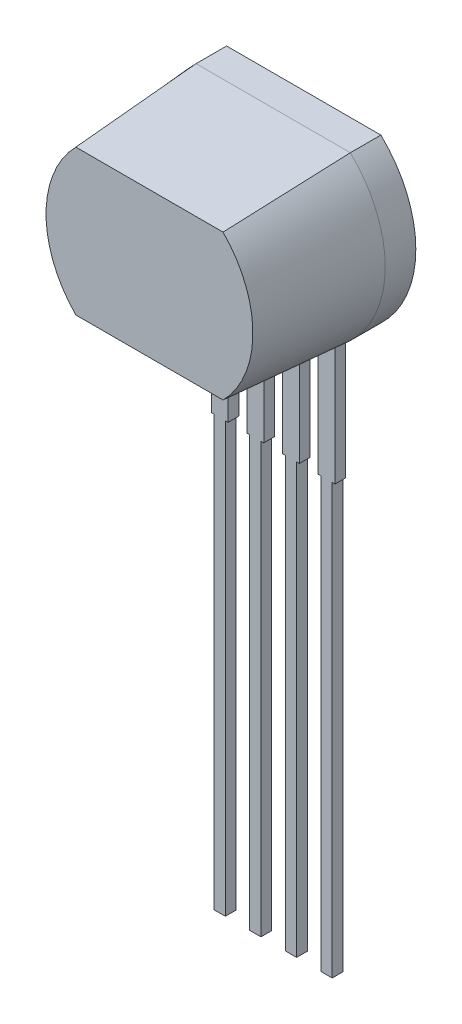
SolidWorks part; units mm, degrees
material "6061-T6 (SS)"
ref_plane "Front Plane" through (0, 0, 0) normal (0, 0, 1) x (1, 0, 0)
ref_plane "Top Plane" through (0, 0, 0) normal (0, 1, 0) x (1, 0, 0)
ref_plane "Right Plane" through (0, 0, 0) normal (1, 0, 0) x (0, 0, -1)
sketch "Sketch1" plane through (0, 0, 0) normal (0, 0, 1) x (1, 0, 0)
  line L0 (-2.75, 2.9) -> (2.75, 2.9)
  line L1 (0, 0) -> (6.1651, 0) construction
  line L2 (0, 0) -> (0, 2.9) construction
  line L3 (-2.75, -2.9) -> (2.75, -2.9)
  arc A0 (-2.75, 2.9) -> (-2.75, -2.9) centre (0.005, 0) ccw
  arc A1 (2.75, 2.9) -> (2.75, -2.9) centre (-0.005, 0) cw
  dimension "D1" = 4
  dimension "D2" = 5.5
  dimension "D3" = 5.8
extrude "Boss-Extrude1" add sketch "Sketch1" along normal blind 4.41 draft 4 and the other way blind 1.09
sketch "Sketch2" plane through (0, 0, 0) normal (0, 0, 1) x (1, 0, 0)
  line L0 (-2.75, -2.9) -> (2.75, -2.9) construction
  line L1 (2.205, -2.9) -> (1.605, -2.9)
  line L2 (2.205, -2.9) -> (2.205, -7.6)
  line L3 (2.205, -7.6) -> (1.605, -7.6) construction
  line L4 (1.605, -2.9) -> (1.605, -7.6)
  line L5 (0.935, -2.9) -> (0.335, -2.9)
  line L6 (0.935, -2.9) -> (0.935, -7.6)
  line L7 (0.335, -2.9) -> (0.335, -7.6)
  line L8 (0.835, -7.6) -> (0.835, -22.9)
  line L9 (0.835, -7.6) -> (0.435, -7.6) construction
  line L10 (0.835, -22.9) -> (0.435, -22.9)
  line L11 (0.435, -7.6) -> (0.435, -22.9)
  line L12 (0.835, -7.6) -> (0.935, -7.6)
  line L13 (0.435, -7.6) -> (0.335, -7.6)
  line L14 (0.935, -7.6) -> (0.335, -7.6) construction
  line L15 (-0.335, -2.9) -> (-0.935, -2.9)
  line L16 (-0.335, -2.9) -> (-0.335, -7.6)
  line L17 (-0.935, -2.9) -> (-0.935, -7.6)
  line L18 (-0.435, -7.6) -> (-0.435, -22.9)
  line L19 (0, -2.9) -> (0, 0) construction
  line L20 (2.105, -7.6) -> (2.105, -22.9)
  line L21 (2.105, -7.6) -> (1.705, -7.6) construction
  line L22 (2.105, -22.9) -> (1.705, -22.9)
  line L23 (1.705, -7.6) -> (1.705, -22.9)
  line L24 (2.105, -7.6) -> (2.205, -7.6)
  line L25 (1.705, -7.6) -> (1.605, -7.6)
  line L26 (-0.435, -7.6) -> (-0.835, -7.6) construction
  line L27 (-0.435, -22.9) -> (-0.835, -22.9)
  line L28 (-0.835, -7.6) -> (-0.835, -22.9)
  line L29 (-0.435, -7.6) -> (-0.335, -7.6)
  line L30 (-0.835, -7.6) -> (-0.935, -7.6)
  line L31 (-0.335, -7.6) -> (-0.935, -7.6) construction
  line L32 (-1.605, -2.9) -> (-2.205, -2.9)
  line L33 (-1.605, -2.9) -> (-1.605, -7.6)
  line L34 (-2.205, -2.9) -> (-2.205, -7.6)
  line L35 (-1.705, -7.6) -> (-1.705, -22.9)
  line L36 (-1.705, -7.6) -> (-2.105, -7.6) construction
  line L37 (-1.705, -22.9) -> (-2.105, -22.9)
  line L38 (-2.105, -7.6) -> (-2.105, -22.9)
  line L39 (-1.705, -7.6) -> (-1.605, -7.6)
  line L40 (-2.105, -7.6) -> (-2.205, -7.6)
  line L41 (-1.605, -7.6) -> (-2.205, -7.6) construction
  line L42 (1.905, -7.6) -> (0.635, -7.6) construction
  line L43 (0.335, -2.9) -> (-0.335, -2.9) construction
  point P12 (0.635, -7.6)
  point P23 (1.905, -7.6)
  point P26 (-0.635, -7.6)
  point P37 (-1.905, -7.6)
  dimension "D2" = 4
  dimension "D3" = 4.7
  dimension "D4" = 0.6
  dimension "D5" = 0.4
  dimension "D1" = 15.3
  dimension "D6" = 1.27
extrude "Boss-Extrude2" add sketch "Sketch2" against normal blind 0.38 separate body
sketch "Sketch3" plane through (0, 0, -1.09) normal (0, 0, -1) x (-1, 0, 0)
  line L0 (-2.501, 0) -> (0, 0) construction
  text T0 "A" font "Century Gothic" height in points 4
  text T1 "ATS605LSG" font "Century Gothic" height in points 3
extrude "Cut-Extrude1" cut sketch "Sketch3" against normal blind 0.01
